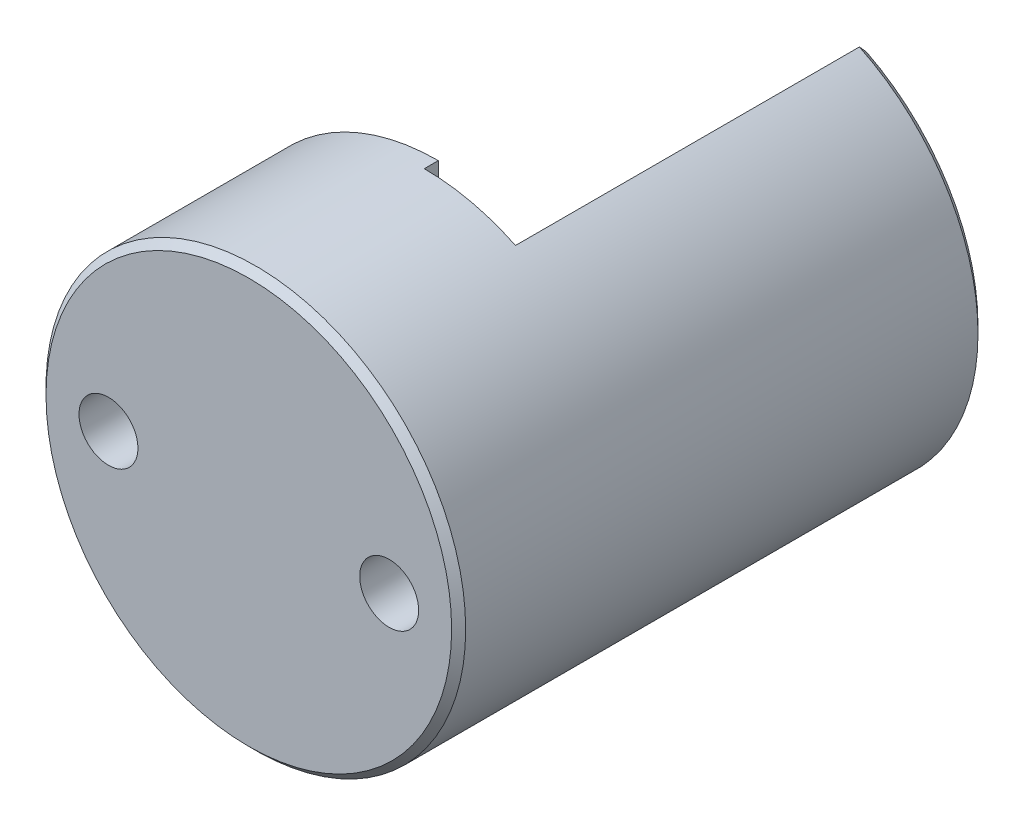
SolidWorks part; units mm, degrees
ref_plane "Front Plane" through (0, 0, 0) normal (0, 0, 1) x (1, 0, 0)
ref_plane "Top Plane" through (0, 0, 0) normal (0, 1, 0) x (1, 0, 0)
ref_plane "Right Plane" through (0, 0, 0) normal (1, 0, 0) x (0, 0, -1)
sketch "Sketch1" plane through (0, 0, 0) normal (0, 0, 1) x (1, 0, 0)
  circle A6 centre (10, 0) radius 2.0999
  circle A7 centre (-10, 0) radius 2.0999
  circle A8 centre (0, 0) radius 14.9496
extrude "Boss-Extrude1" add sketch "Sketch1" against normal blind 7.5 separate body
sketch "Sketch2" plane through (0, 0, -7.5) normal (0, 0, -1) x (-1, 0, 0)
  circle A0 centre (0, 0) radius 14.9496 construction
  circle A1 centre (0, 0) radius 14.9496
extrude "Boss-Extrude2" add sketch "Sketch2" along normal blind 5
sketch "Sketch3" plane through (0, 0, -12.5) normal (0, 0, -1) x (-1, 0, 0)
  line L2 (0, 14.9496) -> (0, -14.9496)
  circle A0 centre (0, 0) radius 14.9496 construction
  arc A2 (0, -14.9496) -> (0, 14.9496) centre (0, 0) ccw
extrude "Boss-Extrude3" add sketch "Sketch3" along normal blind 1
sketch "Sketch4" plane through (0, 0, -12.5) normal (0, 0, -1) x (-1, 0, 0)
  line L1 (-6.4998, -13.4626) -> (-6.4998, 13.4626) construction
  line L2 (-6.4998, 13.4626) -> (-6.4998, -13.4626)
  arc A4 (0, 14.9496) -> (0, -14.9496) centre (0, 0) ccw construction
  arc A5 (-6.4998, 13.4626) -> (-6.4998, -13.4626) centre (0, 0) ccw
  point P2 (-6.4998, -13.5786)
  point P3 (-6.4998, -13.4464)
  point P4 (-6.4998, 13.4338)
  point P5 (-6.4998, 14.1949)
  point P6 (-6.4998, 13.4351)
  point P8 (-6.4998, -13.4338)
extrude "Boss-Extrude4" add sketch "Sketch4" along normal blind 25
sketch "Sketch5" plane through (0, 0, -37.5) normal (0, 0, -1) x (-1, 0, 0)
  circle A1 centre (-10, 0) radius 2.0999
extrude "Cut-Extrude1" cut sketch "Sketch5" against normal blind 7
chamfer "Chamfer2" distance 0.5 angle 45 1 edges at (14.9496, 0, -37.5)
chamfer "Chamfer3" distance 0.5 angle 45 1 edges at (14.9496, 0, 0)
